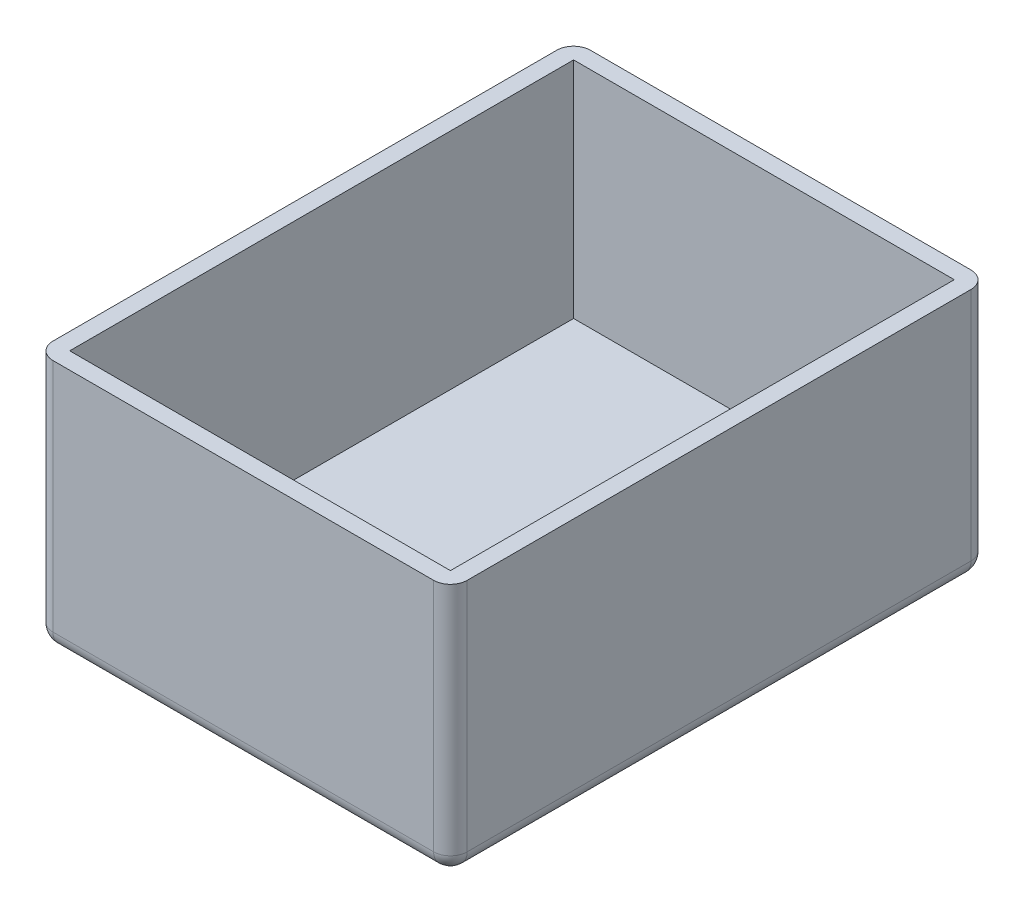
SolidWorks part; units mm, degrees
ref_plane "Front" through (0, 0, 0) normal (0, 0, 1) x (1, 0, 0)
ref_plane "Top" through (0, 0, 0) normal (0, 1, 0) x (1, 0, 0)
ref_plane "Right" through (0, 0, 0) normal (1, 0, 0) x (0, 0, -1)
sketch "Sketch1" plane through (0, 0, 0) normal (0, 1, 0) x (1, 0, 0)
  line L1 (0, 0) -> (74, 0)
  line L2 (0, 0) -> (0, -96)
  line L3 (0, -96) -> (74, -96)
  line L4 (74, 0) -> (74, -96)
  dimension "D1" = 74
  dimension "D2" = 96
extrude "Boss-Extrude1" add sketch "Sketch1" along normal blind 45
sketch "Sketch2" plane through (0, 45, 0) normal (0, 1, 0) x (1, 0, 0)
  line L8 (3, -3) -> (3, -93)
  line L9 (3, -93) -> (71, -93)
  line L10 (71, -93) -> (71, -3)
  line L11 (71, -3) -> (3, -3)
  line L12 (3, -3) -> (3, -93)
  line L13 (3, -93) -> (71, -93)
  line L14 (71, -93) -> (71, -3)
  line L15 (71, -3) -> (3, -3)
  dimension "D1" = 3
extrude "Cut-Extrude1" cut sketch "Sketch2" against normal blind 40
sketch "Sketch3" plane through (0, 0, 0) normal (0, -1, 0) x (1, 0, 0)
  line L0 (0, 96) -> (74, 96) construction
  line L1 (0, 0) -> (0, 96) construction
  circle A0 centre (24, 81.8) radius 3
  circle A1 centre (37, 60) radius 5
  point P4 (0, 0)
  point P7 (37, 96)
  dimension "D1" = 10
  dimension "D2" = 6
  dimension "D3" = 36
  dimension "D4" = 24
  dimension "D5" = 14.2
extrude "Cut-Extrude2" cut sketch "Sketch3" against normal blind 40
fillet "Fillet1" radius 3 8 edges at (0, 22.5, 0) (74, 22.5, 0) (37, 0, 0) (0, 0, 48) (74, 0, 48) (37, 0, 96) (74, 22.5, 96) (0, 22.5, 96)
